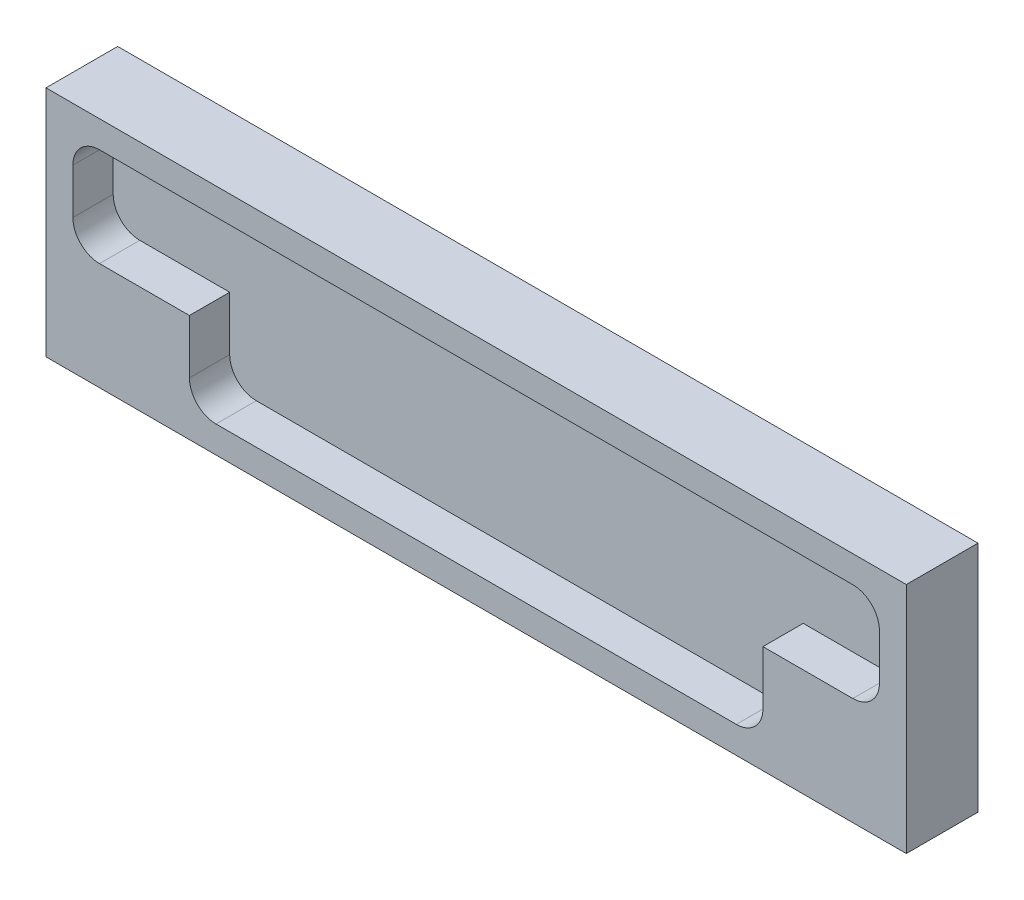
SolidWorks part; units mm, degrees
ref_plane "Front Plane" through (0, 0, 0) normal (0, 0, 1) x (1, 0, 0)
ref_plane "Top Plane" through (0, 0, 0) normal (0, 1, 0) x (1, 0, 0)
ref_plane "Right Plane" through (0, 0, 0) normal (1, 0, 0) x (0, 0, -1)
sketch "Sketch1" plane through (0, 0, 0) normal (0, 0, 1) x (1, 0, 0)
  line L1 (-76.2, 20.6375) -> (76.2, 20.6375)
  line L2 (-76.2, 20.6375) -> (-76.2, -20.6375)
  line L3 (-76.2, -20.6375) -> (76.2, -20.6375)
  line L4 (76.2, 20.6375) -> (76.2, -20.6375)
  line L5 (-76.2, 20.6375) -> (76.2, -20.6375) construction
  line L6 (-76.2, -20.6375) -> (76.2, 20.6375) construction
  point P0 (0, 0)
  dimension "D1" = 152.4
  dimension "D2" = 41.275
extrude "Boss-Extrude1" add sketch "Sketch1" along normal blind 12.7
sketch "Sketch2" plane through (0, 0, 12.7) normal (0, 0, 1) x (1, 0, 0)
  line L0 (76.2, -20.6375) -> (76.2, 20.6375) construction
  line L1 (-66.7184, 15.875) -> (66.7184, 15.875)
  line L2 (-71.4375, 11.1559) -> (-71.4375, 3.1316)
  line L3 (-46.0809, -15.875) -> (46.0809, -15.875)
  line L4 (71.4375, 11.1559) -> (71.4375, 3.1316)
  line L5 (-71.4375, 15.875) -> (67.7595, -15.0577) construction
  line L6 (-67.7595, -15.0577) -> (71.4375, 15.875) construction
  line L7 (76.2, 20.6375) -> (-76.2, 20.6375) construction
  line L8 (50.8, -1.5875) -> (-50.8, -1.5875) construction
  line L9 (50.8, -1.5875) -> (50.8, -11.1559)
  line L10 (50.8, -1.5875) -> (66.7184, -1.5875)
  line L11 (-50.8, -1.5875) -> (-66.7184, -1.5875)
  line L12 (-50.8, -1.5875) -> (-50.8, -11.1559)
  line L13 (-76.2, -20.6375) -> (76.2, -20.6375) construction
  line L14 (-76.2, 20.6375) -> (-76.2, -20.6375) construction
  line L17 (0, -1.5875) -> (0, 15.875) construction
  arc A0 (-66.7184, -1.5875) -> (-71.4375, 3.1316) centre (-66.7184, 3.1316) cw
  arc A1 (-66.7184, 15.875) -> (-71.4375, 11.1559) centre (-66.7184, 11.1559) ccw
  arc A2 (66.7184, 15.875) -> (71.4375, 11.1559) centre (66.7184, 11.1559) cw
  arc A3 (66.7184, -1.5875) -> (71.4375, 3.1316) centre (66.7184, 3.1316) ccw
  arc A4 (50.8, -11.1559) -> (46.0809, -15.875) centre (46.0809, -11.1559) cw
  arc A5 (-46.0809, -15.875) -> (-50.8, -11.1559) centre (-46.0809, -11.1559) cw
  point P0 (0, 0)
  dimension "D7" = 4.7191
  dimension "D1" = 4.7625
  dimension "D2" = 4.7625
  dimension "D3" = 19.05
  dimension "D4" = 25.4
  dimension "D5" = 4.7625
  dimension "D6" = 4.7625
extrude "Cut-Extrude1" cut sketch "Sketch2" against normal blind 7.1374
